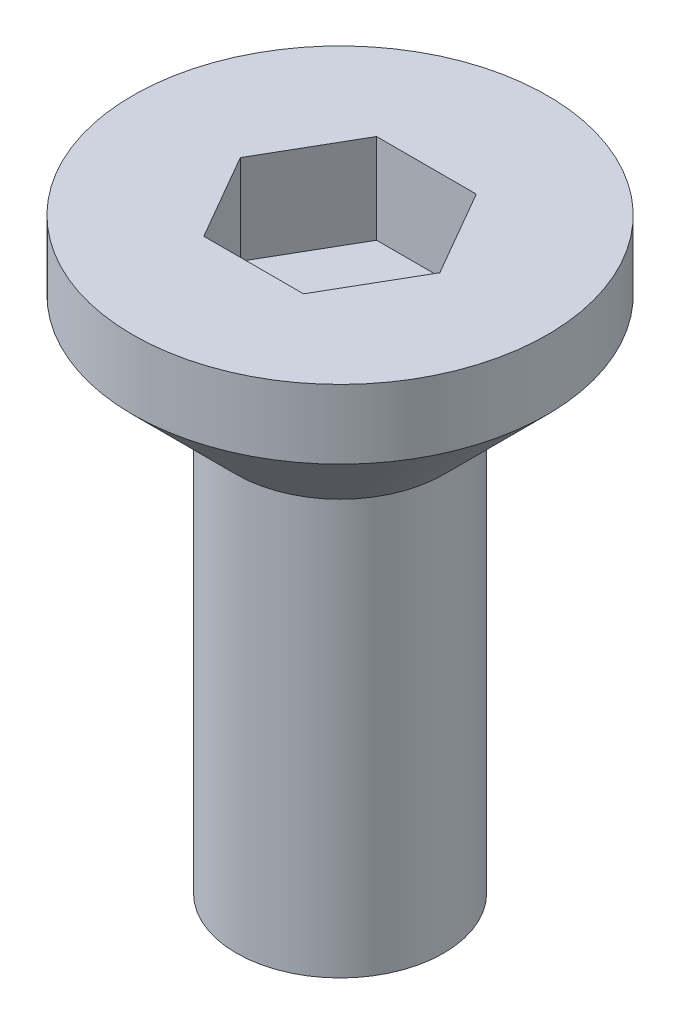
SolidWorks part; units mm, degrees
material "AISI 304"
ref_plane "前视基准面" through (0, 0, 0) normal (0, 0, 1) x (1, 0, 0)
ref_plane "上视基准面" through (0, 0, 0) normal (0, 1, 0) x (1, 0, 0)
ref_plane "右视基准面" through (0, 0, 0) normal (1, 0, 0) x (0, 0, -1)
sketch "草图1" plane through (0, 0, 0) normal (0, 1, 0) x (1, 0, 0)
  circle A0 centre (0, 0) radius 3
  dimension "D1" = 6
extrude "沉头头" add sketch "草图1" along normal blind 2.5
chamfer "倒角1" distance 1.5 angle 45 1 edges at (0, 0, 3)
sketch "草图2" plane through (0, 2.5, 0) normal (0, 1, 0) x (1, 0, 0)
  line L1 (1.4434, 0) -> (0.7217, 1.25)
  line L2 (0.7217, 1.25) -> (-0.7217, 1.25)
  line L3 (-0.7217, 1.25) -> (-1.4434, 0)
  line L4 (-1.4434, 0) -> (-0.7217, -1.25)
  line L5 (-0.7217, -1.25) -> (0.7217, -1.25)
  line L6 (0.7217, -1.25) -> (1.4434, 0)
  circle A0 centre (0, 0) radius 1.25 construction
  dimension "D1" = 2.5
extrude "内六角口" cut sketch "草图2" against normal blind 1.3
sketch "草图3" plane through (0, 0, 0) normal (0, -1, 0) x (1, 0, 0)
  circle A0 centre (0, 0) radius 1.5
  dimension "D1" = 3
extrude "螺纹长" add sketch "草图3" along normal blind 6
